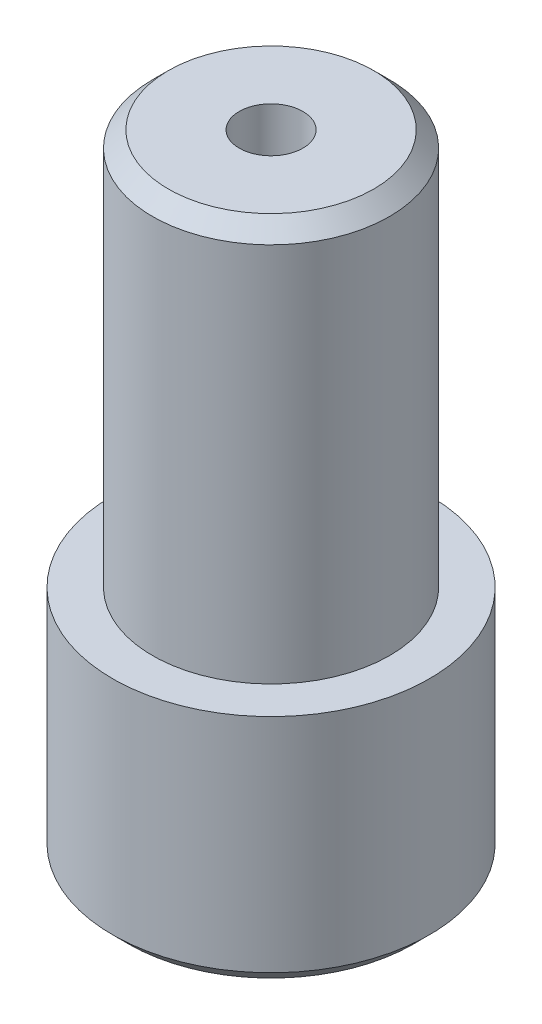
SolidWorks part; units mm, degrees
ref_plane "Front Plane" through (0, 0, 0) normal (0, 0, 1) x (1, 0, 0)
ref_plane "Top Plane" through (0, 0, 0) normal (0, 1, 0) x (1, 0, 0)
ref_plane "Right Plane" through (0, 0, 0) normal (1, 0, 0) x (0, 0, -1)
sketch "Sketch1" plane through (0, 0, 0) normal (0, 0, 1) x (1, 0, 0)
  line L0 (0, 0) -> (12.7, 0)
  line L1 (12.7, 0) -> (12.7, 19.05)
  line L2 (12.7, 19.05) -> (9.4996, 19.05)
  line L3 (9.4996, 19.05) -> (9.4996, 50.8)
  line L4 (9.4996, 50.8) -> (0, 50.8)
  line L5 (0, 50.8) -> (0, 0)
  point P6 (9.4996, 34.925)
  point P8 (0, 41.3705)
  dimension "D1" = 12.7
  dimension "D2" = 19.05
  dimension "D3" = 9.4996
  dimension "D4" = 31.75
revolve "Revolve1" add sketch "Sketch1" angle 360 about L5
chamfer "Chamfer1" distance 1.27 angle 45 2 edges at (-12.7, 0, 0) (-9.4996, 50.8, 0)
hole_wizard "1/4-20 Tapped Hole1" positions "Sketch2" profile "Sketch4" tap size "1/4-20" standard "ANSI Inch"
sketch "Sketch2" plane through (0, 50.8, 0) normal (0, 1, 0) x (1, 0, 0)
  point P0 (0, 0)
sketch "Sketch4" plane through (0, 50.8, 0) normal (1, 0, 0) x (0, 0, 1)
  line L0 (0, 0) -> (0, 18.0438)
  line L1 (0, 18.0438) -> (2.5527, 16.51)
  line L2 (2.5527, 16.51) -> (2.5527, 0)
  line L5 (2.5527, 0) -> (0, 0)
  line L10 (0, 18.0438) -> (-2.5527, 16.51) construction
  line L11 (0, -6.35) -> (0, 107.95) construction
  dimension "Tap Drill Dia." = 5.1054
  dimension "Tap Drill Depth" = 16.51
  dimension "Drill Angle" = 118
cosmetic thread "Hole Thread1" parameters "D1"=12.7, "D2"=6.35
equation "\"D3@Sketch1\"=.748/2"
